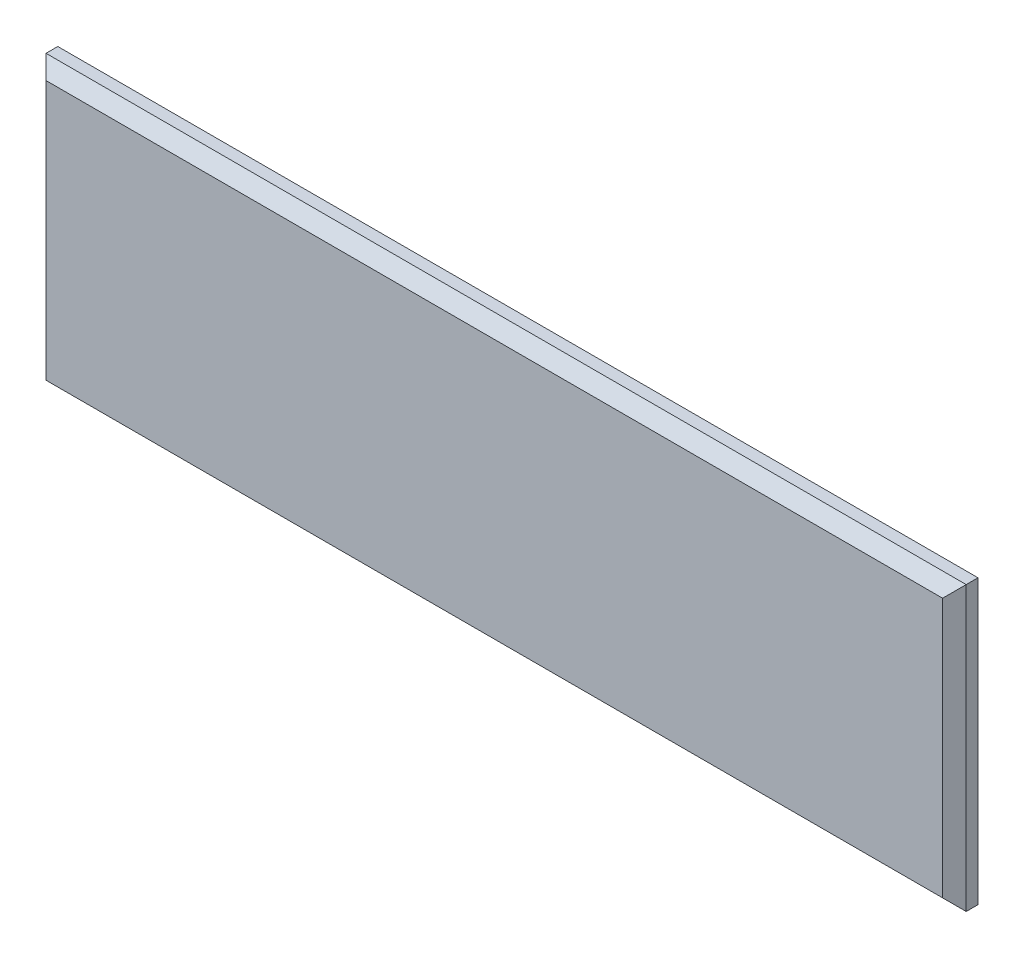
SolidWorks part; units mm, degrees
ref_plane "Top Plane" through (0, 0, 0) normal (0, 0, 1) x (1, 0, 0)
ref_plane "Front Plane" through (0, 0, 0) normal (0, 1, 0) x (1, 0, 0)
ref_plane "Right Plane" through (0, 0, 0) normal (1, 0, 0) x (0, 0, -1)
sketch "Profile Sketch" plane through (0, 0, 0) normal (0, 0, 1) x (1, 0, 0)
  line L1 (-495.3, -152.4) -> (495.3, -152.4)
  line L2 (-495.3, -152.4) -> (-495.3, 152.4)
  line L3 (-495.3, 152.4) -> (495.3, 152.4)
  line L4 (495.3, -152.4) -> (495.3, 152.4)
  line L5 (-495.3, -152.4) -> (495.3, 152.4) construction
  line L6 (-495.3, 152.4) -> (495.3, -152.4) construction
  point P0 (0, 0)
  dimension "D1" = 990.6
  dimension "D2" = 304.8
extrude "Profile Extrude" add sketch "Profile Sketch" along normal blind 25.4
chamfer "Edge Chamfer" distance 12.7 angle 45 4 edges at (0, -152.4, 25.4) (-495.3, 0, 25.4) (0, 152.4, 25.4) (495.3, 0, 25.4)
sketch "Centering Sketch" plane through (0, 0, 25.4) normal (0, 0, 1) x (1, 0, 0)
  line L0 (-495.3, 0) -> (495.3, 0) construction
  line L4 (495.3, -152.4) -> (495.3, 152.4)
  line L5 (-495.3, -152.4) -> (495.3, -152.4)
  line L6 (-495.3, 152.4) -> (-495.3, -152.4)
  line L7 (495.3, 152.4) -> (-495.3, 152.4)
  line L8 (495.3, -152.4) -> (495.3, 152.4) construction
  line L10 (-495.3, 152.4) -> (-495.3, -152.4) construction
  point P6 (0, 0)
  dimension "D1" = 0
